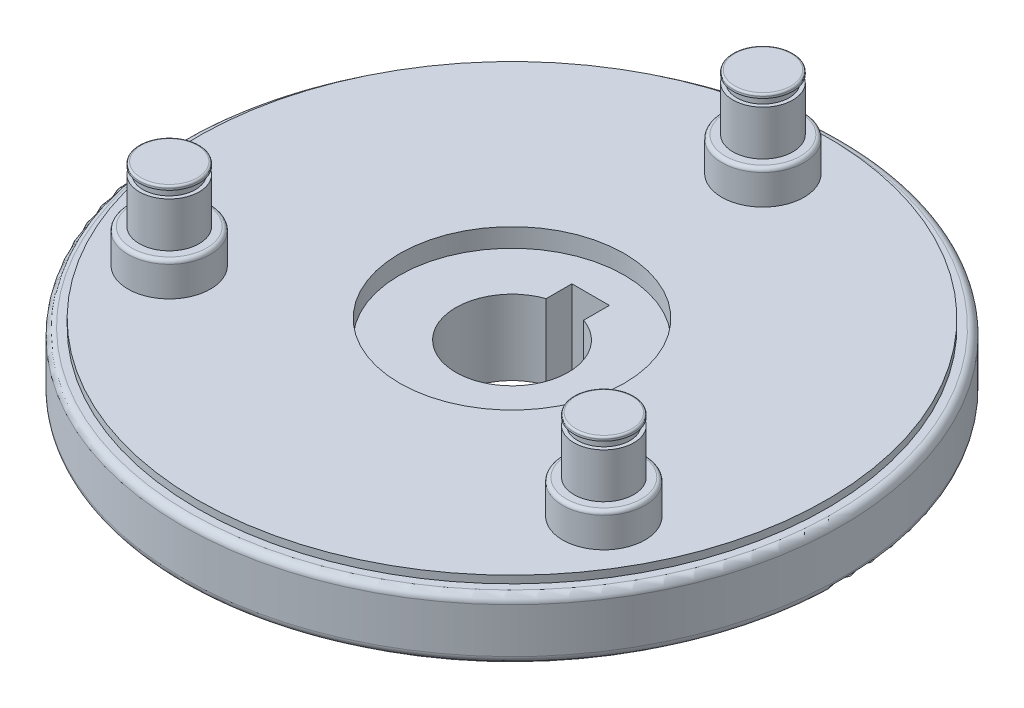
SolidWorks part; units mm, degrees
material "1060 Alloy"
ref_plane "Front Plane" through (0, 0, 0) normal (0, 0, 1) x (1, 0, 0)
ref_plane "Top Plane" through (0, 0, 0) normal (0, 1, 0) x (1, 0, 0)
ref_plane "Right Plane" through (0, 0, 0) normal (1, 0, 0) x (0, 0, -1)
sketch "Sketch1" plane through (0, 0, 0) normal (0, 1, 0) x (1, 0, 0)
  circle A0 centre (0, 0) radius 44
  dimension "D1" = 88
extrude "Boss-Extrude1" add sketch "Sketch1" along normal blind 10
sketch "Sketch2" plane through (0, 10, 0) normal (0, 1, 0) x (1, 0, 0)
  circle A2 centre (0, 0) radius 42
  circle A3 centre (0, 0) radius 42
  circle A5 centre (0, 0) radius 44
  circle A6 centre (0, 0) radius 44
  dimension "D1" = 2
  dimension "D2" = 0
extrude "Cut-Extrude1" cut sketch "Sketch2" against normal blind 1
ref_plane "Plane1" through (0, 5, 0) normal (0, -1, 0) x (-1, 0, 0)
mirror "Mirror1" about plane through (0, 5, 0) normal (0, -1, 0) of "Cut-Extrude1"
fillet "Fillet1" radius 1 2 edges at (0, 1, 44) (0, 9, 44)
sketch "Sketch3" plane through (0, 10, 0) normal (0, 1, 0) x (1, 0, 0)
  circle A0 centre (0, 0) radius 15
  dimension "D1" = 30
extrude "Cut-Extrude2" cut sketch "Sketch3" against normal blind 2.5
sketch "Sketch4" plane through (0, 7.5, 0) normal (0, 1, 0) x (1, 0, 0)
  circle A0 centre (0, 0) radius 7.5
  dimension "D1" = 15
extrude "Cut-Extrude3" cut sketch "Sketch4" against normal blind 65.5
sketch "Sketch5" plane through (0, 7.5, 0) normal (0, 1, 0) x (1, 0, 0)
  line L0 (0, 0) -> (0, 15) construction
  line L2 (-2.5, 4.5) -> (2.5, 4.5)
  line L3 (-2.5, 4.5) -> (-2.5, 10.5)
  line L4 (-2.5, 10.5) -> (2.5, 10.5)
  line L5 (2.5, 4.5) -> (2.5, 10.5)
  line L6 (-2.5, 4.5) -> (2.5, 10.5) construction
  line L7 (-2.5, 10.5) -> (2.5, 4.5) construction
  circle A0 centre (0, 0) radius 15 construction
  point P6 (0, 7.5)
  dimension "D1" = 5
  dimension "D2" = 3
extrude "Cut-Extrude4" cut sketch "Sketch5" against normal blind 65.5
sketch "Sketch7" plane through (0, 0, 0) normal (0, -1, 0) x (1, 0, 0)
  circle A0 centre (0, 0) radius 15
  dimension "D1" = 30
extrude "Cut-Extrude5" cut sketch "Sketch7" against normal blind 2
sketch "Sketch8" plane through (0, 2, 0) normal (0, -1, 0) x (1, 0, 0)
  line L9 (2.5, -10.5) -> (2.5, -7.0711)
  line L10 (-2.5, -10.5) -> (2.5, -10.5)
  line L11 (-2.5, -7.0711) -> (-2.5, -10.5)
  line L12 (2.5, -10.5) -> (2.5, -7.0711)
  line L13 (-2.5, -10.5) -> (2.5, -10.5)
  line L14 (-2.5, -7.0711) -> (-2.5, -10.5)
  circle A3 centre (0, 0) radius 13.5
  circle A4 centre (0, 0) radius 13.5
  arc A9 (2.5, -7.0711) -> (-2.5, -7.0711) centre (0, 0) ccw
  arc A10 (2.5, -7.0711) -> (-2.5, -7.0711) centre (0, 0) ccw
  dimension "D1" = 1.5
  dimension "D2" = 0
extrude "Boss-Extrude2" add sketch "Sketch8" along normal blind 4.5
chamfer "Chamfer1" distance 1.5 angle 45 1 edges at (0, -2.5, -13.5)
sketch "Sketch9" plane through (0, 10, 0) normal (0, 1, 0) x (1, 0, 0)
  line L0 (0, 33.5) -> (0, 42) construction
  circle A0 centre (0, 33.5) radius 5.5
  circle A4 centre (0, 0) radius 42 construction
  dimension "D2" = 11
  dimension "D1" = 0
  dimension "D3" = 8.5
extrude "Boss-Extrude3" add sketch "Sketch9" along normal blind 12
sketch "Sketch10" plane through (0, 22, 0) normal (0, 1, 0) x (1, 0, 0)
  circle A0 centre (0, 33.5) radius 4
  circle A3 centre (0, 33.5) radius 5.5
  circle A4 centre (0, 33.5) radius 5.5
  dimension "D1" = 8
  dimension "D2" = 0
extrude "Cut-Extrude6" cut sketch "Sketch10" against normal blind 7.5
fillet "Fillet2" radius 0.5 1 edges at (0, 14.5, -28)
sketch "Sketch11" plane through (0, 22, 0) normal (0, 1, 0) x (1, 0, 0)
  circle A2 centre (0, 33.5) radius 3.5
  circle A3 centre (0, 33.5) radius 3.5
  circle A5 centre (0, 33.5) radius 4
  circle A6 centre (0, 33.5) radius 4
  dimension "D1" = 0.5
  dimension "D2" = 0
extrude "Cut-Extrude7" cut sketch "Sketch11" against normal blind 1.5
sketch "Sketch12" plane through (0, 22, 0) normal (0, 1, 0) x (1, 0, 0)
  circle A2 centre (0, 33.5) radius 4
  circle A3 centre (0, 33.5) radius 4
  dimension "D1" = 0.5
extrude "Boss-Extrude4" add sketch "Sketch12" against normal blind 0.5
fillet "Fillet3" radius 0.25 1 edges at (0, 22, -29.5)
pattern_circular "CirPattern1" count 3 over 360 about axis through (0, 0, 0) along (0, 1, 0) of "Boss-Extrude3", "Cut-Extrude6", "Cut-Extrude7", "Boss-Extrude4", "Fillet3", "Fillet2"
